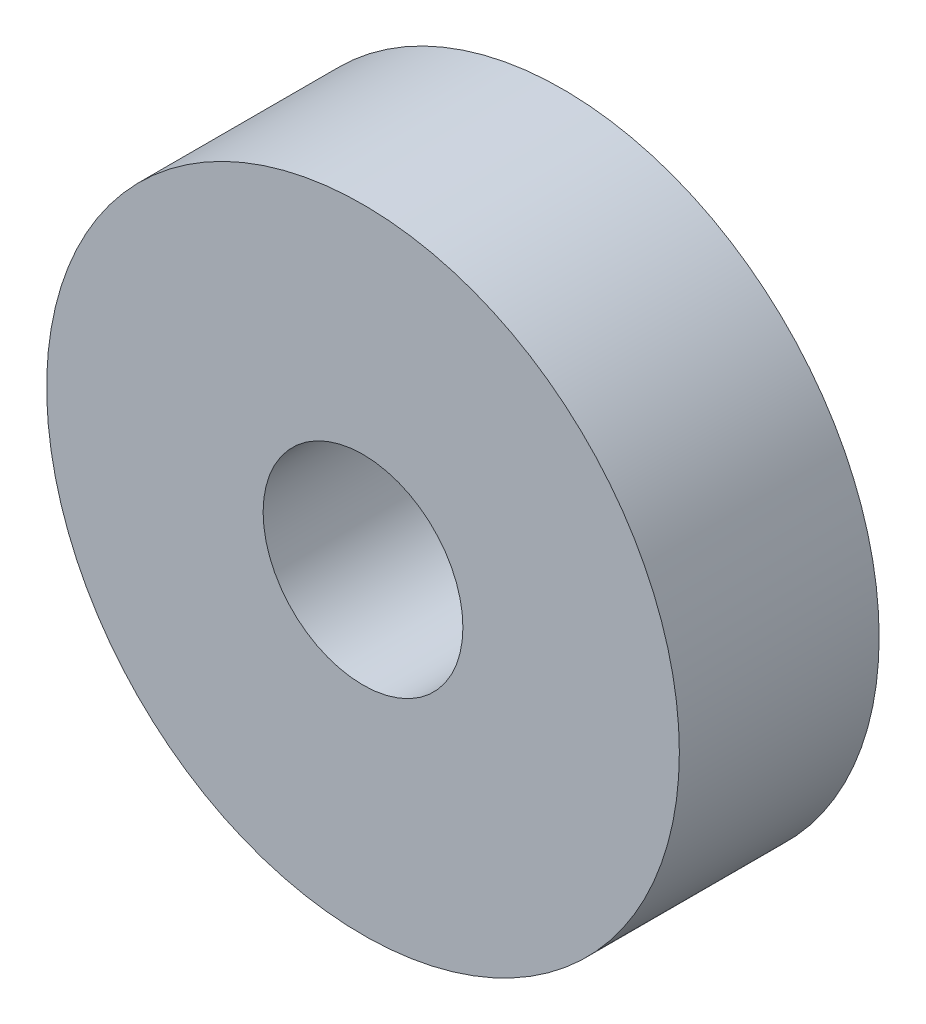
SolidWorks part; units mm, degrees
ref_plane "Plan de face" through (0, 0, 0) normal (0, 0, 1) x (1, 0, 0)
ref_plane "Plan de dessus" through (0, 0, 0) normal (0, 1, 0) x (1, 0, 0)
ref_plane "Plan de droite" through (0, 0, 0) normal (1, 0, 0) x (0, 0, -1)
sketch "Esquisse1" plane through (0, 0, 0) normal (0, 0, 1) x (1, 0, 0)
  circle A0 centre (0, 0) radius 3
  circle A1 centre (0, 0) radius 9.5
extrude "Extrusion1" add sketch "Esquisse1" along normal blind 6
